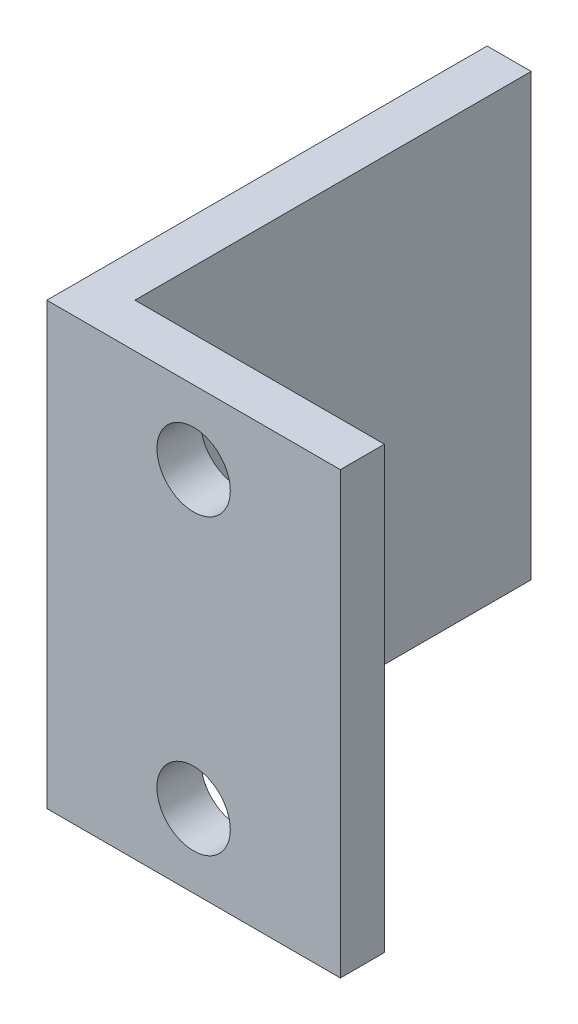
SolidWorks part; units mm, degrees
ref_plane "Front Plane" through (0, 0, 0) normal (0, 0, 1) x (1, 0, 0)
ref_plane "Top Plane" through (0, 0, 0) normal (0, 1, 0) x (1, 0, 0)
ref_plane "Right Plane" through (0, 0, 0) normal (1, 0, 0) x (0, 0, -1)
sketch "Sketch1" plane through (0, 0, 0) normal (0, 1, 0) x (1, 0, 0)
  line L0 (0, 30) -> (0, 0)
  line L1 (0, 0) -> (20, 0)
  line L2 (20, 0) -> (20, 3)
  line L3 (20, 3) -> (3, 3)
  line L4 (3, 3) -> (3, 30)
  line L5 (3, 30) -> (0, 30)
  dimension "D1" = 20
  dimension "D2" = 3
  dimension "D3" = 3
  dimension "D4" = 30
extrude "Boss-Extrude1" add sketch "Sketch1" along normal blind 30
sketch "Sketch2" plane through (0, 0, 0) normal (0, 0, 1) x (1, 0, 0)
  line L0 (0, 15) -> (20, 15) construction
  line L1 (0, 30) -> (0, 0) construction
  line L2 (20, 30) -> (20, 0) construction
  circle A0 centre (10, 25) radius 2.5
  circle A1 centre (10, 5) radius 2.5
  dimension "D1" = 10
  dimension "D2" = 10
  dimension "D3" = 5
extrude "Cut-Extrude1" cut sketch "Sketch2" against normal through all
